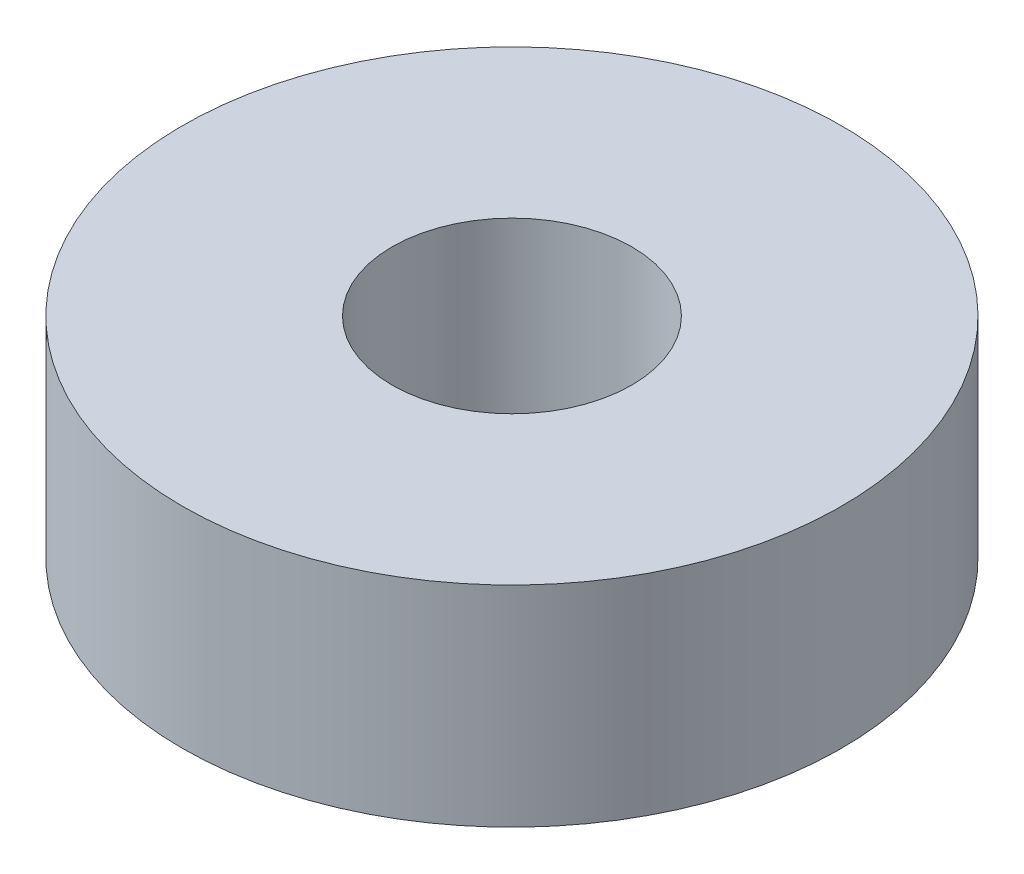
SolidWorks part; units mm, degrees
ref_plane "Front Plane" through (0, 0, 0) normal (0, 0, 1) x (1, 0, 0)
ref_plane "Top Plane" through (0, 0, 0) normal (0, 1, 0) x (1, 0, 0)
ref_plane "Right Plane" through (0, 0, 0) normal (1, 0, 0) x (0, 0, -1)
sketch "Sketch1" plane through (0, 0, 0) normal (0, 1, 0) x (1, 0, 0)
  circle A0 centre (0, 0) radius 4
  circle A1 centre (0, 0) radius 11
  dimension "D1" = 8
  dimension "D2" = 22
extrude "Boss-Extrude1" add sketch "Sketch1" along normal blind 7
